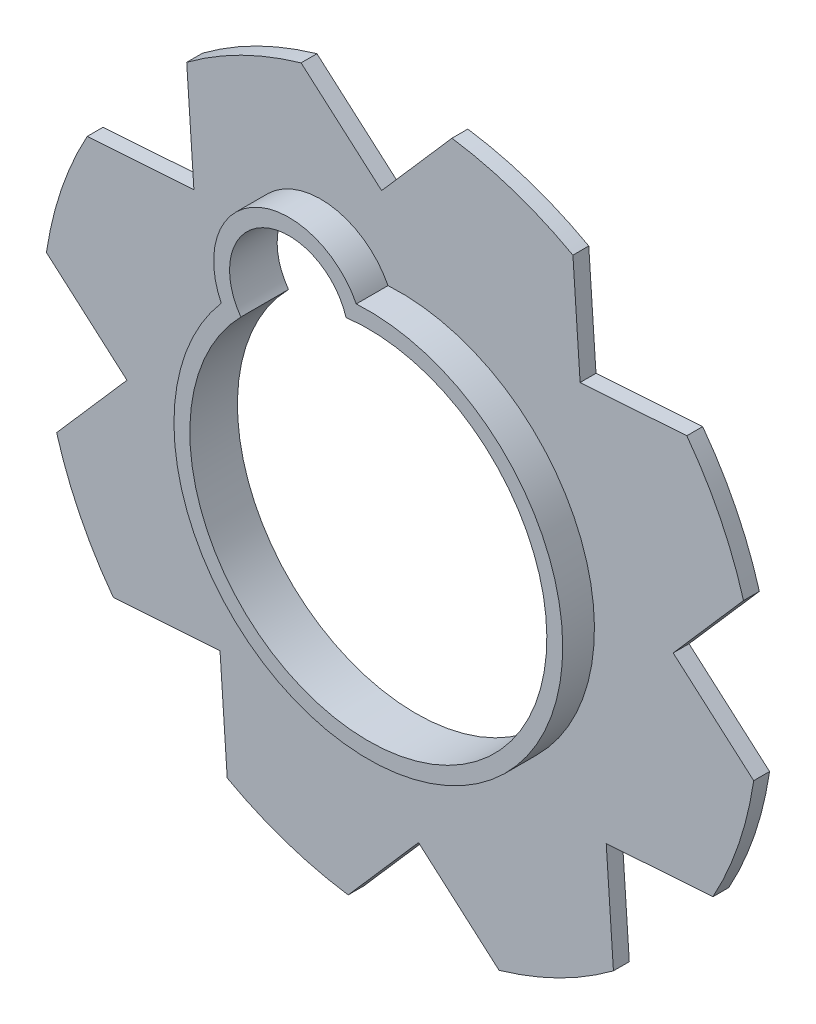
SolidWorks part; units mm, degrees
ref_plane "Front" through (0, 0, 0) normal (0, 0, 1) x (1, 0, 0)
ref_plane "Top" through (0, 0, 0) normal (0, 1, 0) x (1, 0, 0)
ref_plane "Right" through (0, 0, 0) normal (1, 0, 0) x (0, 0, -1)
sketch "Sketch1" plane through (0, 0, 0) normal (0, 0, 1) x (1, 0, 0)
  line L16 (-6.5396, -44.5728) -> (2.3265, -34.4215)
  line L17 (2.3265, -34.4215) -> (12.4778, -43.2875)
  line L18 (26.8936, -36.1419) -> (25.9847, -22.6946)
  line L19 (25.9847, -22.6946) -> (39.432, -21.7857)
  line L20 (44.5728, -6.5396) -> (34.4215, 2.3265)
  line L21 (34.4215, 2.3265) -> (43.2875, 12.4778)
  line L22 (36.1419, 26.8936) -> (22.6946, 25.9847)
  line L23 (22.6946, 25.9847) -> (21.7857, 39.432)
  line L24 (6.5396, 44.5728) -> (-2.3265, 34.4215)
  line L25 (-2.3265, 34.4215) -> (-12.4778, 43.2875)
  line L26 (-26.8936, 36.1419) -> (-25.9847, 22.6946)
  line L27 (-25.9847, 22.6946) -> (-39.432, 21.7857)
  line L28 (-44.5728, 6.5396) -> (-34.4215, -2.3265)
  line L29 (-34.4215, -2.3265) -> (-43.2875, -12.4778)
  line L30 (-36.1419, -26.8936) -> (-22.6946, -25.9847)
  line L31 (-22.6946, -25.9847) -> (-21.7857, -39.432)
  line L32 (-6.5396, -44.5728) -> (2.3265, -34.4215)
  line L33 (2.3265, -34.4215) -> (12.4778, -43.2875)
  line L34 (26.8936, -36.1419) -> (25.9847, -22.6946)
  line L35 (25.9847, -22.6946) -> (39.432, -21.7857)
  line L36 (44.5728, -6.5396) -> (34.4215, 2.3265)
  line L37 (34.4215, 2.3265) -> (43.2875, 12.4778)
  line L38 (36.1419, 26.8936) -> (22.6946, 25.9847)
  line L39 (22.6946, 25.9847) -> (21.7857, 39.432)
  line L40 (6.5396, 44.5728) -> (-2.3265, 34.4215)
  line L41 (-2.3265, 34.4215) -> (-12.4778, 43.2875)
  line L42 (-26.8936, 36.1419) -> (-25.9847, 22.6946)
  line L43 (-25.9847, 22.6946) -> (-39.432, 21.7857)
  line L44 (-44.5728, 6.5396) -> (-34.4215, -2.3265)
  line L45 (-34.4215, -2.3265) -> (-43.2875, -12.4778)
  line L46 (-36.1419, -26.8936) -> (-22.6946, -25.9847)
  line L47 (-22.6946, -25.9847) -> (-21.7857, -39.432)
  line L80 (-20.0073, 40.3635) -> (0, 0) construction
  arc A0 (-16.0632, 15.7551) -> (-2.8116, 22.3236) centre (0, 0) ccw
  arc A9 (12.4778, -43.2875) -> (26.8936, -36.1419) centre (0, 0) ccw
  arc A10 (39.432, -21.7857) -> (44.5728, -6.5396) centre (0, 0) ccw
  arc A11 (43.2875, 12.4778) -> (36.1419, 26.8936) centre (0, 0) ccw
  arc A12 (21.7857, 39.432) -> (6.5396, 44.5728) centre (0, 0) ccw
  arc A13 (-12.4778, 43.2875) -> (-26.8936, 36.1419) centre (0, 0) ccw
  arc A14 (-39.432, 21.7857) -> (-44.5728, 6.5396) centre (0, 0) ccw
  arc A15 (-43.2875, -12.4778) -> (-36.1419, -26.8936) centre (0, 0) ccw
  arc A16 (-21.7857, -39.432) -> (-6.5396, -44.5728) centre (0, 0) ccw
  arc A17 (12.4778, -43.2875) -> (26.8936, -36.1419) centre (0, 0) ccw
  arc A18 (39.432, -21.7857) -> (44.5728, -6.5396) centre (0, 0) ccw
  arc A19 (43.2875, 12.4778) -> (36.1419, 26.8936) centre (0, 0) ccw
  arc A20 (21.7857, 39.432) -> (6.5396, 44.5728) centre (0, 0) ccw
  arc A21 (-12.4778, 43.2875) -> (-26.8936, 36.1419) centre (0, 0) ccw
  arc A22 (-39.432, 21.7857) -> (-44.5728, 6.5396) centre (0, 0) ccw
  arc A23 (-43.2875, -12.4778) -> (-36.1419, -26.8936) centre (0, 0) ccw
  arc A24 (-21.7857, -39.432) -> (-6.5396, -44.5728) centre (0, 0) ccw
  arc A41 (-2.8116, 22.3236) -> (-16.0632, 15.7551) centre (-9.9925, 20.1593) ccw
  dimension "D2" = 45
  dimension "D3" = 15
  dimension "D1" = 0
extrude "Boss-Extrude1" add sketch "Sketch1" along normal blind 2
sketch "Sketch2" plane through (0, 0, 2) normal (0, 0, 1) x (1, 0, 0)
  arc A0 (-16.0632, 15.7551) -> (-2.8116, 22.3236) centre (0, 0) ccw construction
  arc A1 (-2.8116, 22.3236) -> (-16.0632, 15.7551) centre (-9.9925, 20.1593) ccw construction
  arc A2 (-16.0632, 15.7551) -> (-2.8116, 22.3236) centre (0, 0) ccw
  arc A3 (-2.8116, 22.3236) -> (-16.0632, 15.7551) centre (-9.9925, 20.1593) ccw
  arc A4 (-1.5182, 24.4529) -> (-18.5409, 16.0151) centre (-9.9925, 20.1593) ccw
  arc A5 (-18.5409, 16.0151) -> (-1.5182, 24.4529) centre (0, 0) ccw
  dimension "D1" = 2
extrude "Boss-Extrude2" add sketch "Sketch2" along normal blind 4
